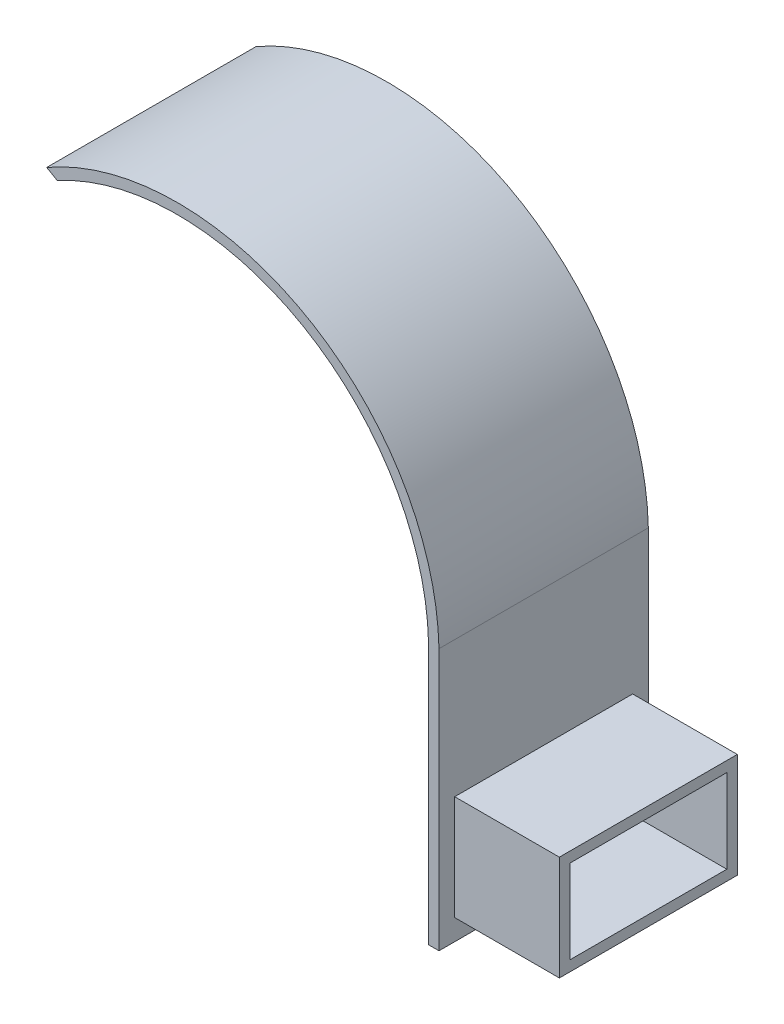
SolidWorks part; units mm, degrees
ref_plane "Front Plane" through (0, 0, 0) normal (0, 0, 1) x (1, 0, 0)
ref_plane "Top Plane" through (0, 0, 0) normal (0, 1, 0) x (1, 0, 0)
ref_plane "Right Plane" through (0, 0, 0) normal (1, 0, 0) x (0, 0, -1)
sketch "Sketch2" plane through (0, 0, 0) normal (0, 0, 1) x (1, 0, 0)
  circle A0 centre (0, 0) radius 24
  circle A1 centre (0, 0) radius 25
  dimension "D1" = 50
  dimension "D2" = 48
extrude "Boss-Extrude1" add sketch "Sketch2" along normal blind 20
sketch "Sketch3" plane through (0, 0, 20) normal (0, 0, 1) x (1, 0, 0)
  line L0 (-12.4884, 21.6573) -> (25, 0)
  line L1 (25, 0) -> (47.9006, -51.2076)
  line L2 (47.9006, -51.2076) -> (-94.1978, -17.7373)
  line L3 (-94.1978, -17.7373) -> (-12.4884, 21.6573)
  circle A0 centre (0, 0) radius 25 construction
extrude "Cut-Extrude1" cut sketch "Sketch3" against normal through all
sketch "Sketch4" plane through (0, 0, 20) normal (0, 0, 1) x (1, 0, 0)
  line L1 (23.9929, 0.5818) -> (25.2738, 0.5818)
  line L2 (23.9929, 0.5818) -> (23.9929, -0.1457)
  line L3 (23.9929, -0.1457) -> (25.2738, -0.1457)
  line L4 (25.2738, 0.5818) -> (25.2738, -0.1457)
extrude "Cut-Extrude2" cut sketch "Sketch4" against normal through all
sketch "Sketch5" plane through (0, 0.5818, 0) normal (0, -1, 0) x (1, 0, 0)
  line L1 (23.9929, 20) -> (24.9932, 20)
  line L2 (23.9929, 20) -> (23.9929, 0)
  line L3 (23.9929, 0) -> (24.9932, 0)
  line L4 (24.9932, 20) -> (24.9932, 0)
extrude "Boss-Extrude2" add sketch "Sketch5" along normal blind 25
sketch "Sketch6" plane through (24.9932, 0, 0) normal (1, 0, 0) x (0, 0, -1)
  line L0 (0, -24.4182) -> (-20, -24.4182) construction
  line L1 (-17.5, -21.4182) -> (-2.5, -21.4182)
  line L2 (-17.5, -21.4182) -> (-17.5, -13.4182)
  line L3 (-17.5, -13.4182) -> (-2.5, -13.4182)
  line L4 (-2.5, -21.4182) -> (-2.5, -13.4182)
  line L5 (-20, -24.4182) -> (-20, 0.5818) construction
  dimension "D1" = 15
  dimension "D2" = 8
  dimension "D3" = 3
  dimension "D4" = 2.5
extrude "Cut-Extrude3" cut sketch "Sketch6" against normal through all
sketch "Sketch7" plane through (24.9932, 0, 0) normal (1, 0, 0) x (0, 0, -1)
  line L0 (-17.5, -13.4182) -> (-17.5, -21.4182) construction
  line L1 (-18.5, -22.4182) -> (-1.5, -22.4182)
  line L2 (-18.5, -22.4182) -> (-18.5, -12.4182)
  line L3 (-18.5, -12.4182) -> (-1.5, -12.4182)
  line L4 (-1.5, -22.4182) -> (-1.5, -12.4182)
  line L5 (-2.5, -13.4182) -> (-17.5, -13.4182) construction
  line L7 (-2.5, -21.4182) -> (-2.5, -13.4182) construction
  line L9 (-17.5, -21.4182) -> (-2.5, -21.4182) construction
  line L16 (-17.5, -13.4182) -> (-17.5, -21.4182)
  line L17 (-17.5, -21.4182) -> (-2.5, -21.4182)
  line L18 (-2.5, -21.4182) -> (-2.5, -13.4182)
  line L19 (-2.5, -13.4182) -> (-17.5, -13.4182)
  dimension "D1" = 17
  dimension "D2" = 10
  dimension "D3" = 1
  dimension "D4" = 1
extrude "Boss-Extrude3" add sketch "Sketch7" along normal blind 10
